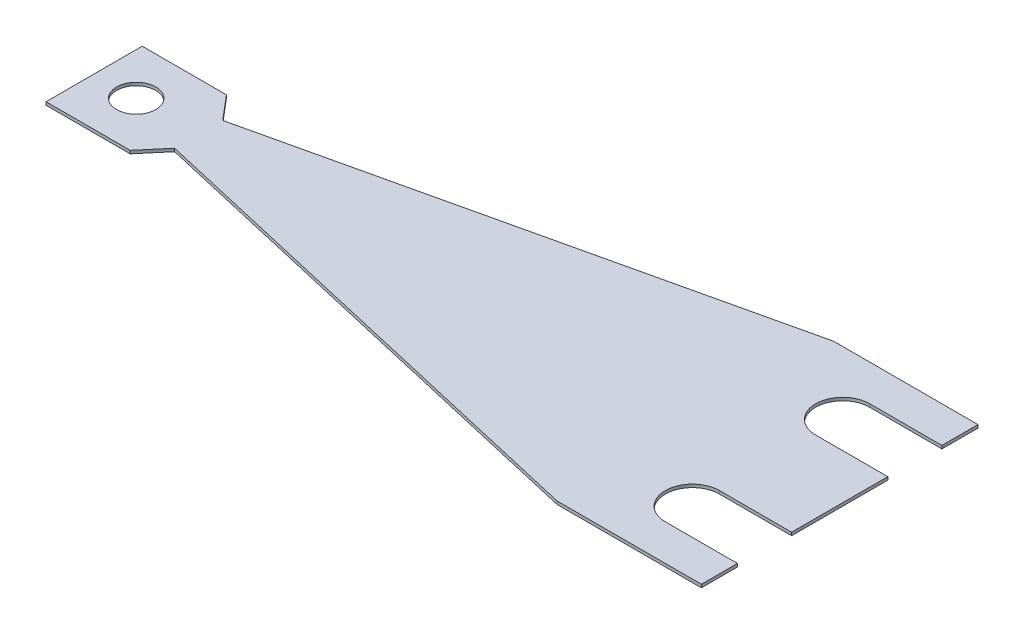
SolidWorks part; units mm, degrees
material "Beryllium Copper, UNS C17200"
ref_plane "Front" through (0, 0, 0) normal (0, 0, 1) x (1, 0, 0)
ref_plane "Top" through (0, 0, 0) normal (0, 1, 0) x (1, 0, 0)
ref_plane "Right" through (0, 0, 0) normal (1, 0, 0) x (0, 0, -1)
sketch "Sketch1" plane through (0, 0, 0) normal (0, 1, 0) x (1, 0, 0)
  line L0 (0, -11.5) -> (0, 11.5)
  line L1 (0, 11.5) -> (-12, 11.5)
  line L2 (-12, 11.5) -> (-53.3043, 2)
  line L3 (-53.3043, 2) -> (-55, 4)
  line L4 (-55, 4) -> (-62, 4)
  line L5 (-62, 4) -> (-62, -4)
  line L6 (-55, -4) -> (-62, -4)
  line L7 (0, 0) -> (-62, 0) construction
  line L8 (-53.3043, -2) -> (-55, -4)
  line L9 (-12, -11.5) -> (-53.3043, -2)
  line L10 (0, -11.5) -> (-12, -11.5)
  dimension "D1" = 11.5
  dimension "D2" = 2
  dimension "D3" = 12
  dimension "D4" = 7
  dimension "D5" = 4
  dimension "D6" = 50
  dimension "D7" = 8.6957
extrude "Extrude1" add sketch "Sketch1" along normal blind 0.254
sketch "Sketch2" plane through (0, 0.254, 0) normal (0, 1, 0) x (1, 0, 0)
  line L0 (0, -11.5) -> (0, 11.5) construction
  line L1 (-6, 4) -> (0, 4)
  line L2 (0, 4) -> (0, 8.5)
  line L3 (0, 8.5) -> (-6, 8.5)
  line L4 (0, 0) -> (-62, 0) construction
  line L5 (-62, 4) -> (-62, -4) construction
  line L6 (0, -8.5) -> (-6, -8.5)
  line L7 (0, -4) -> (0, -8.5)
  line L8 (-6, -4) -> (0, -4)
  arc A0 (-6, 8.5) -> (-6, 4) centre (-6, 6.25) ccw
  arc A1 (-6, -8.5) -> (-6, -4) centre (-6, -6.25) cw
  dimension "D1" = 4.5
  dimension "D2" = 6.25
  dimension "D3" = 6
extrude "Extrude2" cut sketch "Sketch2" against normal through all
sketch "Sketch3" plane through (0, 0.254, 0) normal (0, 1, 0) x (1, 0, 0)
  line L0 (-62, 4) -> (-62, -4) construction
  circle A0 centre (-58.5, 0) radius 1.63
  point P2 (-62, 0)
  dimension "D1" = 3.26
  dimension "D2" = 3.5
extrude "Extrude3" cut sketch "Sketch3" against normal through all
equation "\"D7@Sketch1\" = \"D2@Sketch1\" * \"D6@Sketch1\" / \"D1@Sketch1\""
